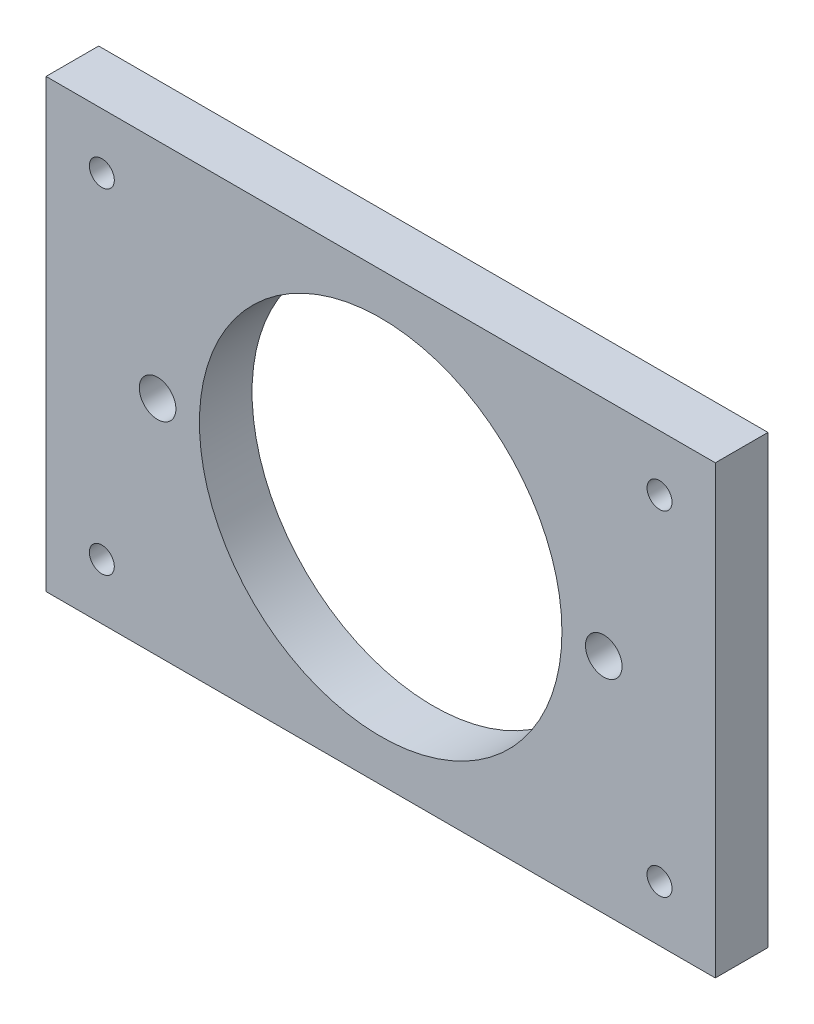
SolidWorks part; units mm, degrees
ref_plane "Front Plane" through (0, 0, 0) normal (0, 0, 1) x (1, 0, 0)
ref_plane "Top Plane" through (0, 0, 0) normal (0, 1, 0) x (1, 0, 0)
ref_plane "Right Plane" through (0, 0, 0) normal (1, 0, 0) x (0, 0, -1)
sketch "Sketch1" plane through (0, 0, 0) normal (0, 0, 1) x (1, 0, 0)
  line L0 (0, 0) -> (-25.4, 0) construction
  line L1 (-38.1, 25.4) -> (38.1, 25.4)
  line L2 (-38.1, 25.4) -> (-38.1, -25.4)
  line L3 (-38.1, -25.4) -> (38.1, -25.4)
  line L4 (38.1, 25.4) -> (38.1, -25.4)
  circle A0 centre (0, 0) radius 20.6375
  circle A1 centre (-25.4, 0) radius 2.0828
  circle A2 centre (25.4, 0) radius 2.0828
  circle A3 centre (-31.75, 19.05) radius 1.4224
  circle A4 centre (-31.75, -19.05) radius 1.4224
  circle A5 centre (31.75, -19.05) radius 1.4224
  circle A6 centre (31.75, 19.05) radius 1.4224
  dimension "D1" = 41.275
  dimension "D6" = 4.1656
  dimension "D9" = 2.8448
  dimension "D10" = 31.75
  dimension "D2" = 76.2
  dimension "D3" = 50.8
  dimension "D4" = 38.1
  dimension "D5" = 25.4
  dimension "D7" = 25.4
  dimension "D8" = 25.4
  dimension "D11" = 63.5
  dimension "D12" = 38.1
  dimension "D13" = 19.05
extrude "Boss-Extrude1" add sketch "Sketch1" along normal blind 5.9944
